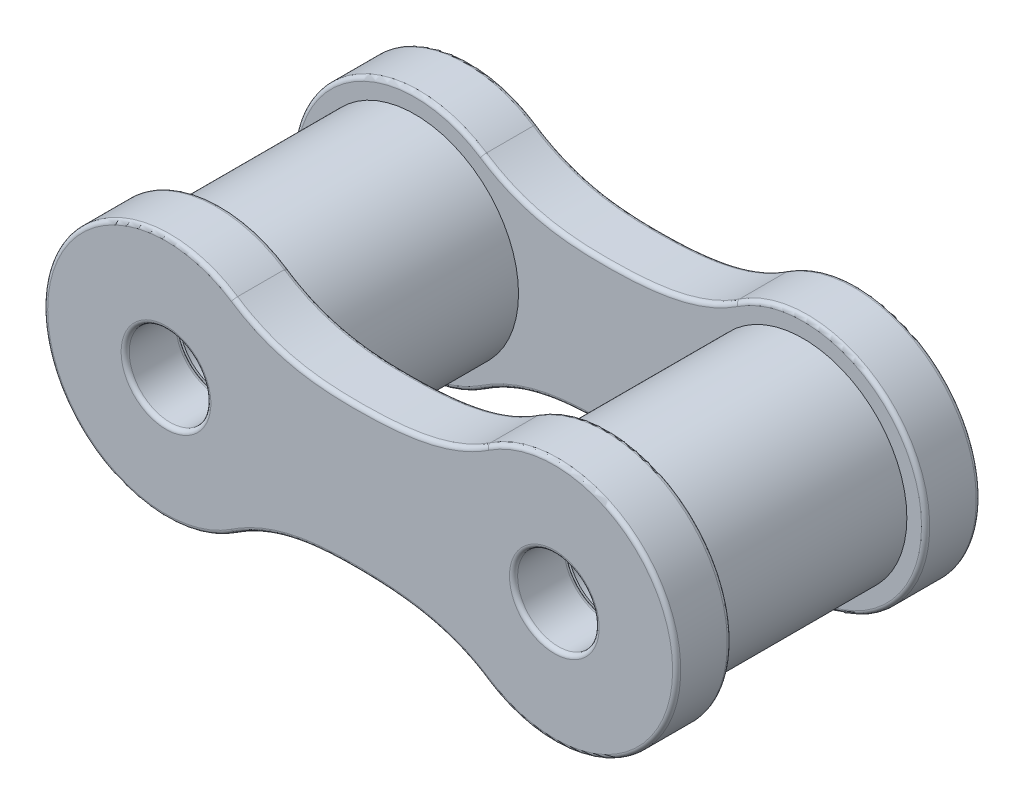
SolidWorks part; units mm, degrees
ref_plane "Front Plane" through (0, 0, 0) normal (0, 0, 1) x (1, 0, 0)
ref_plane "Top Plane" through (0, 0, 0) normal (0, 1, 0) x (1, 0, 0)
ref_plane "Right Plane" through (0, 0, 0) normal (1, 0, 0) x (0, 0, -1)
sketch "Sketch2" plane through (0, 0, 0) normal (0, 0, 1) x (1, 0, 0)
  line L0 (-7.76, 0) -> (7.76, 0) construction
  line L1 (0, -2.5) -> (0, 2.5) construction
  line L2 (-3.1017, 2.5) -> (3.1017, 2.5) construction
  arc A0 (-3.1017, 2.5) -> (-3.1017, -2.5) centre (-4.76, 0) ccw
  circle A1 centre (-4.76, 0) radius 1
  circle A2 centre (4.76, 0) radius 1
  arc A3 (3.1017, 2.5) -> (3.1017, -2.5) centre (4.76, 0) cw
  spline S0 degree 3 poles (-3.1017, 2.5) (-2.1036, 1.8379) (-0.0309, 1.6416) (2.1654, 1.879) (3.1017, 2.5) knots 0 0 0 0 0.5 1 1 1 1
  spline S1 degree 3 poles (-3.1017, -2.5) (-2.1036, -1.8379) (-0.0309, -1.6416) (2.1654, -1.879) (3.1017, -2.5) knots 0 0 0 0 0.5 1 1 1 1
  point P4 (0, 0)
  point P8 (0, 0)
  point P14 (3.2139, 2.6157)
  point P17 (3.3871, 2.6674)
  point P18 (-2.9426, 2.3868)
  point P19 (0, 1.3388)
  point P20 (2.8804, 2.3382)
  point P21 (-0.3436, 0.9761)
  point P22 (3.0104, 2.437)
  point P23 (0, 1.0545)
  point P24 (-3.1045, 2.5019)
  point P25 (0, 1.4515)
  point P27 (0, 1.5)
  point P28 (-3.1555, 2.5349)
  point P32 (10.2062, 0)
  dimension "D1" = 6
  dimension "D2" = 2
  dimension "D5" = 2.5
  dimension "D3" = 9.52
  dimension "D4" = 1.75
extrude "Boss-Extrude1" add sketch "Sketch2" along normal blind 1.3425
fillet "Fillet1" radius 0.1 12 edges at (3.76, 0, 0) (-3.76, 0, 0) (7.76, 0, 0) (-7.76, 0, 0) (3.76, 0, 1.3425) (-3.76, 0, 1.3425) (7.76, 0, 1.3425) (-7.76, 0, 1.3425)
sketch "Sketch3" plane through (0, 0, 1.3425) normal (0, 0, 1) x (1, 0, 0)
  line L0 (0, 0) -> (0, 1.65) construction
  circle A0 centre (-4.76, 0) radius 2.54
  circle A2 centre (-4.76, 0) radius 1 construction
  circle A3 centre (-4.76, 0) radius 1
  circle A4 centre (4.76, 0) radius 2.54
  circle A5 centre (4.76, 0) radius 1
  spline S0 degree 3 poles (3.157, 2.4167) (2.692, 2.1083) (2.1807, 1.9158) (1.0955, 1.6877) (0.5479, 1.6553) (-0.2724, 1.6474) (-0.546, 1.6517) (-1.094, 1.6909) (-1.3705, 1.7263) (-1.9082, 1.8413) (-2.1702, 1.9208) (-2.6785, 2.1312) (-2.9253, 2.263) (-3.157, 2.4167) knots 0 0 0 0 0.25 0.25 0.5 0.5 0.625 0.625 0.75 0.75 0.875 0.875 1 1 1 1 construction
  dimension "D1" = 5.08
extrude "Boss-Extrude2" add sketch "Sketch3" along normal blind 4.76
ref_plane "Plane1" through (0, 0, 3.7225) normal (0, 0, 1) x (1, 0, 0)
mirror "Mirror1" about plane through (0, 0, 3.7225) normal (0, 0, 1) of bodies 102
sketch "Sketch5" plane through (0, 0, 3.7225) normal (0, 0, 1) x (1, 0, 0)
  line L0 (-190.5, 0) -> (190.5, 0)
  line L2 (-193.992, -51.6) -> (193.992, -51.6) construction
  line L3 (0, 0) -> (0, -64.6) construction
  arc A0 (-190.5, 0) -> (-193.992, -51.6) centre (-190.5, -25.9182) ccw
  arc A1 (193.992, -51.6) -> (190.5, 0) centre (190.5, -25.9182) ccw
  spline S0 degree 3 poles (-193.992, -51.6) (-129.4767, -60.3723) (4.024, -68.2806) (121.4286, -61.4666) (193.992, -51.6) knots 0 0 0 0 0.5 1 1 1 1
  point P3 (0, 0)
  point P4 (0, 0)
  point P6 (-193.992, -51.6)
  point P8 (-193.992, -51.6)
  point P14 (0, -105.4247)
  point P15 (0, -74.838)
  point P16 (194.0724, -51.5889)
  point P17 (0, -64.1992)
  point P18 (-198.1738, -50.6743)
  point P19 (0, -63.8667)
  point P20 (-193.8911, -51.6135)
  point P21 (0, -63.2018)
  point P22 (0, -64.8666)
  dimension "D2" = 51.8363
  dimension "D1" = 381
  dimension "D3" = 51.6
  dimension "D4" = 13
